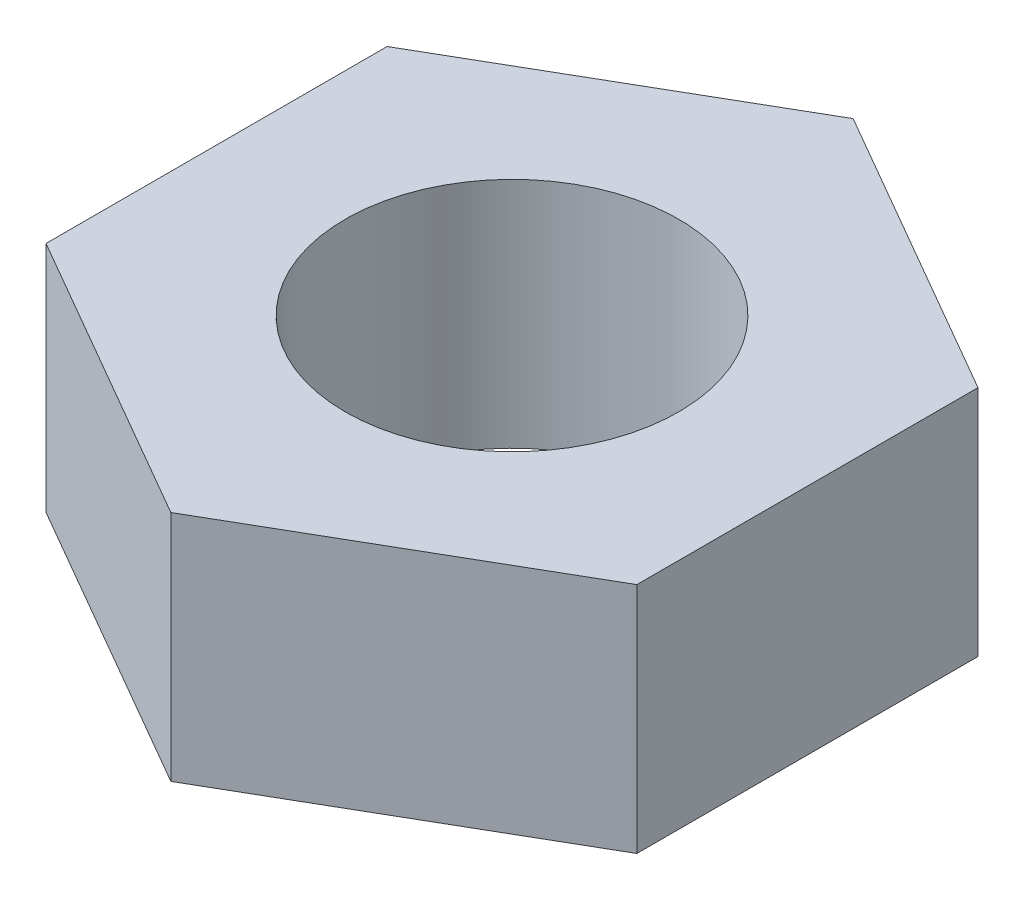
SolidWorks part; units mm, degrees
ref_plane "Front Plane" through (0, 0, 0) normal (0, 0, 1) x (1, 0, 0)
ref_plane "Top Plane" through (0, 0, 0) normal (0, 1, 0) x (1, 0, 0)
ref_plane "Right Plane" through (0, 0, 0) normal (1, 0, 0) x (0, 0, -1)
sketch "Sketch1" plane through (0, 0, 0) normal (0, 1, 0) x (1, 0, 0)
  line L1 (0, 4.9075) -> (-4.25, 2.4537)
  line L2 (-4.25, 2.4537) -> (-4.25, -2.4537)
  line L3 (-4.25, -2.4537) -> (0, -4.9075)
  line L4 (0, -4.9075) -> (4.25, -2.4537)
  line L5 (4.25, -2.4537) -> (4.25, 2.4537)
  line L6 (4.25, 2.4537) -> (0, 4.9075)
  circle A0 centre (0, 0) radius 4.25 construction
  dimension "D1" = 8.5
extrude "Boss-Extrude1" add sketch "Sketch1" along normal blind 3.35
sketch "Sketch2" plane through (0, 3.35, 0) normal (0, 1, 0) x (1, 0, 0)
  circle A0 centre (0, 0) radius 2.4
  dimension "D1" = 4.8
extrude "Cut-Extrude1" cut sketch "Sketch2" against normal up to next
